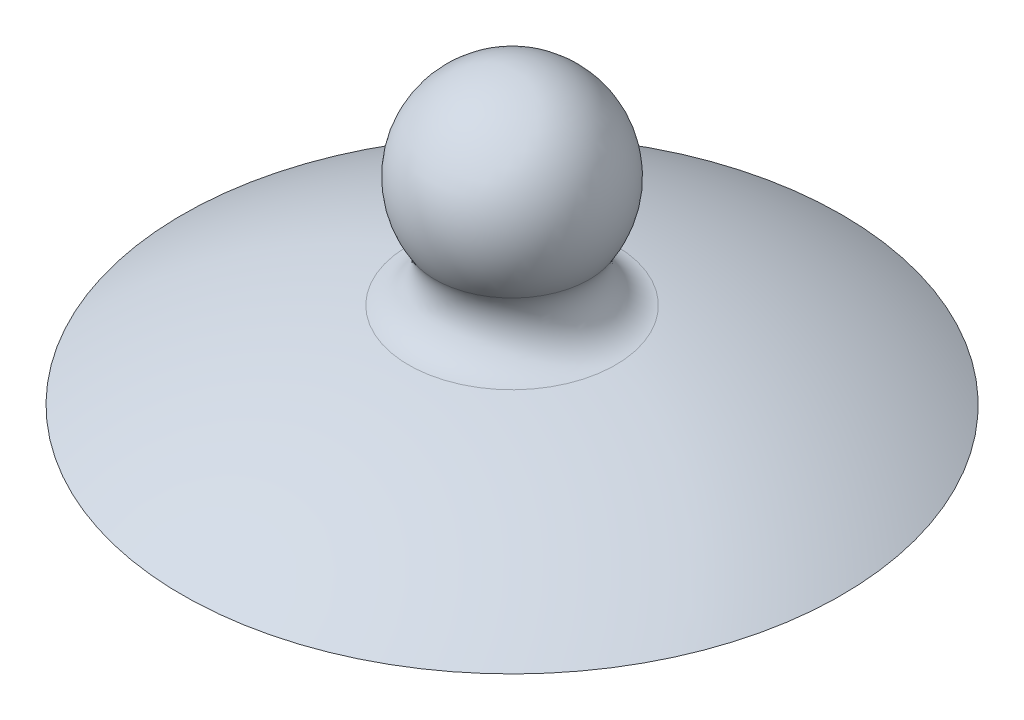
SolidWorks part; units mm, degrees
ref_plane "Front Plane" through (0, 0, 0) normal (0, 0, 1) x (1, 0, 0)
ref_plane "Top Plane" through (0, 0, 0) normal (0, 1, 0) x (1, 0, 0)
ref_plane "Right Plane" through (0, 0, 0) normal (1, 0, 0) x (0, 0, -1)
sketch "Sketch1" plane through (0, 0, 0) normal (0, 0, 1) x (1, 0, 0)
  line L0 (0, 0) -> (0, 15) construction
  line L1 (-25, 0) -> (17.5, 0)
  line L2 (20.5, 0) -> (20.5, -3)
  line L3 (20.5, -3) -> (17.5, -3)
  line L4 (17.5, -3) -> (17.5, 0)
  line L5 (0, 15) -> (0, 25.502) construction
  line L6 (0, 0) -> (0, 22)
  line L7 (20.5, 0) -> (25, 0)
  arc A0 (25, 0) -> (7.8495, 6.5404) centre (0, -39.7995) ccw
  arc A1 (5.8454, 11.1488) -> (0, 22) centre (0, 15) ccw
  arc A2 (5.8454, 11.1488) -> (7.8495, 6.5404) centre (8.3505, 9.4983) ccw
  arc A3 (0, 7.2005) -> (-25, 0) centre (0, -39.7995) ccw construction
  point P8 (0, 0)
  dimension "D5" = 47
  dimension "D7" = 14
  dimension "D8" = 6
  dimension "D1" = 50
  dimension "D2" = 3
  dimension "D3" = 3
  dimension "D4" = 4.5
  dimension "D6" = 15
revolve "Revolve1" add sketch "Sketch1" angle 360 about L0
